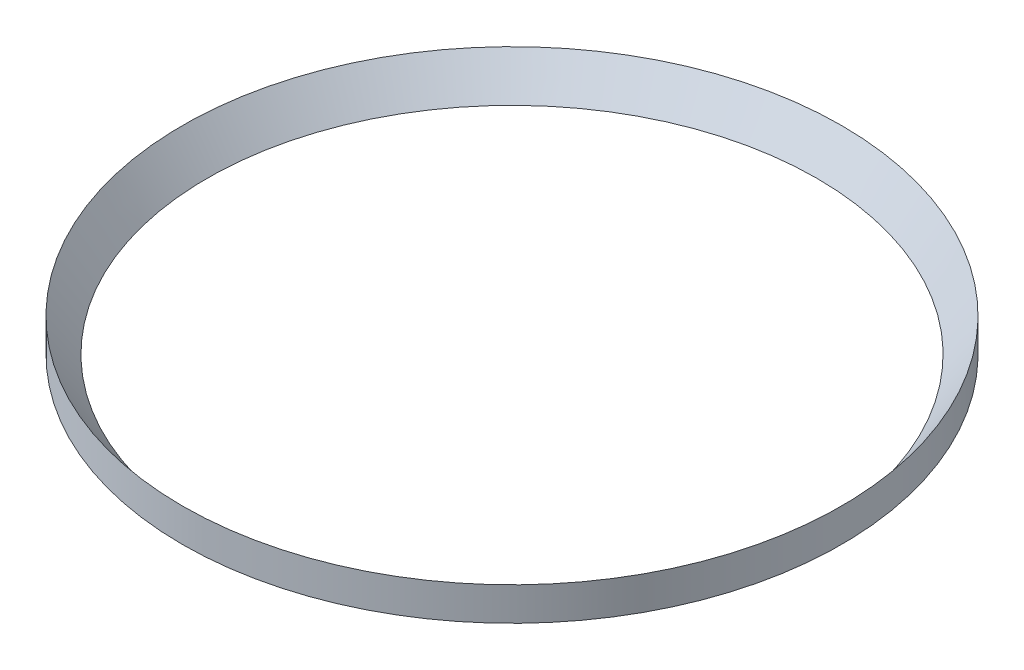
SolidWorks part; units mm, degrees
ref_plane "Front Plane" through (0, 0, 0) normal (0, 0, 1) x (1, 0, 0)
ref_plane "Top Plane" through (0, 0, 0) normal (0, 1, 0) x (1, 0, 0)
ref_plane "Right Plane" through (0, 0, 0) normal (1, 0, 0) x (0, 0, -1)
sketch "Sketch1" plane through (0, 0, 0) normal (0, 0, 1) x (1, 0, 0)
  line L0 (0, 0) -> (0, 40.1643) construction
  line L1 (-16, 0) -> (-16, 1.62)
  line L2 (-16, 1.62) -> (-14.8, 0)
  line L3 (-14.8, 0) -> (-16, 0)
  dimension "D1" = 1.62
  dimension "D2" = 1.2
  dimension "D3" = 16
revolve "Revolve1" add sketch "Sketch1" angle 360 about L0
